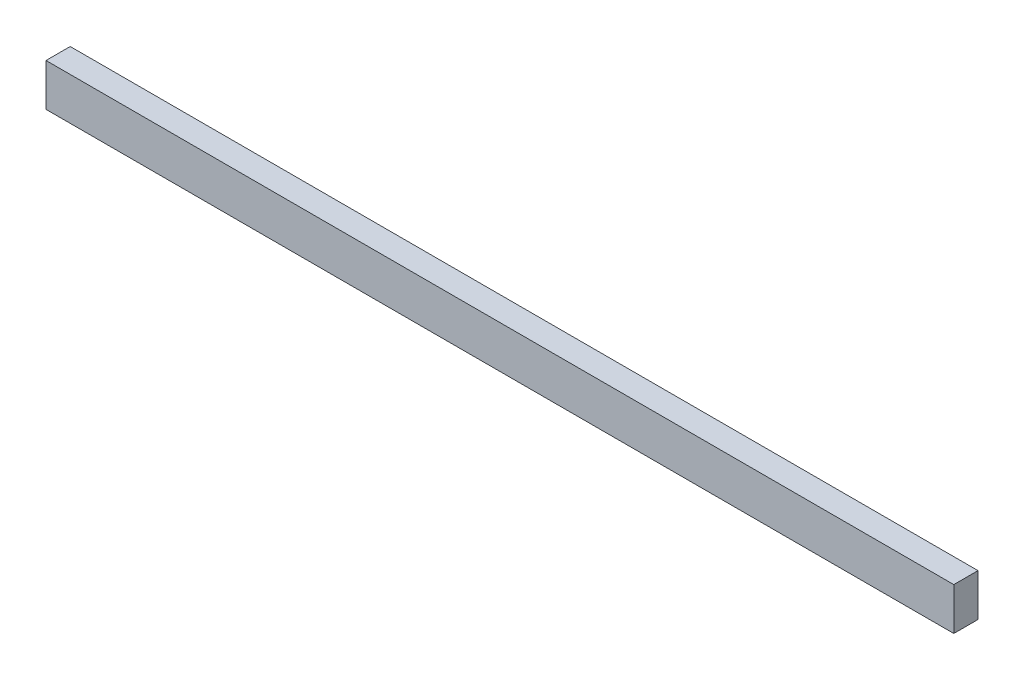
SolidWorks part; units mm, degrees
material "Дуб"
ref_plane "Спереди" through (0, 0, 0) normal (0, 0, 1) x (1, 0, 0)
ref_plane "Сверху" through (0, 0, 0) normal (0, 1, 0) x (1, 0, 0)
ref_plane "Справа" through (0, 0, 0) normal (1, 0, 0) x (0, 0, -1)
sketch "Эскиз1" plane through (0, 0, 0) normal (0, 0, 1) x (1, 0, 0)
  line L1 (-750, 35) -> (750, 35)
  line L2 (-750, 35) -> (-750, -35)
  line L3 (-750, -35) -> (750, -35)
  line L4 (750, 35) -> (750, -35)
  line L5 (-750, 35) -> (750, -35) construction
  line L6 (-750, -35) -> (750, 35) construction
  point P0 (0, 0)
  dimension "D1" = 1500
  dimension "D2" = 70
extrude "Бобышка-Вытянуть1" add sketch "Эскиз1" along normal blind 40
